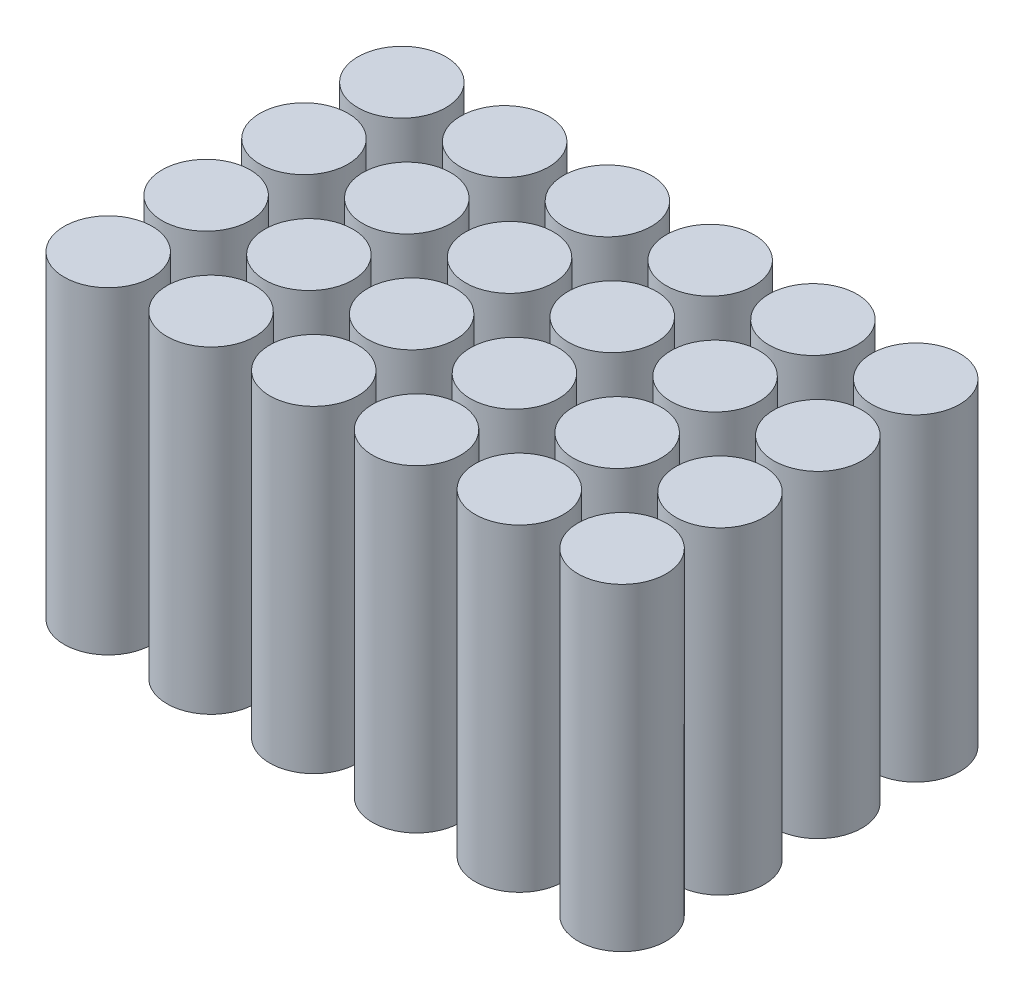
SolidWorks part; units mm, degrees
material "Li-ion 18650 equivalent"
ref_plane "Front Plane" through (0, 0, 0) normal (0, 0, 1) x (1, 0, 0)
ref_plane "Top Plane" through (0, 0, 0) normal (0, 1, 0) x (1, 0, 0)
ref_plane "Right Plane" through (0, 0, 0) normal (1, 0, 0) x (0, 0, -1)
sketch "Sketch2" plane through (0, 0, 0) normal (0, 1, 0) x (1, 0, 0)
  line L0 (0, -38.3676) -> (0, 38.3676) construction
  line L1 (-63.7189, 0) -> (63.7189, 0) construction
  circle A0 centre (-10.5, -10) radius 9
  circle A1 centre (10.5, -10) radius 9
  circle A2 centre (31.5, -10) radius 9
  circle A3 centre (52.5, -10) radius 9
  circle A4 centre (10.5, 10) radius 9
  circle A5 centre (31.5, 10) radius 9
  circle A6 centre (52.5, 10) radius 9
  circle A7 centre (10.5, 30) radius 9
  circle A8 centre (31.5, 30) radius 9
  circle A9 centre (52.5, 30) radius 9
  circle A10 centre (-10.5, 10) radius 9
  circle A11 centre (-10.5, 30) radius 9
  circle A12 centre (-10.5, -30) radius 9
  circle A13 centre (52.5, -30) radius 9
  circle A14 centre (31.5, -30) radius 9
  circle A15 centre (10.5, -30) radius 9
  circle A16 centre (-52.5, -30) radius 9
  circle A17 centre (-52.5, -10) radius 9
  circle A18 centre (-52.5, 10) radius 9
  circle A19 centre (-52.5, 30) radius 9
  circle A20 centre (-31.5, -30) radius 9
  circle A21 centre (-31.5, -10) radius 9
  circle A22 centre (-31.5, 10) radius 9
  circle A23 centre (-31.5, 30) radius 9
  point P4 (0, 0)
  point P8 (0, 0)
  point P9 (-10.5, -1)
  point P10 (-1.5, -10)
  dimension "D1" = 18
  dimension "D2" = 1
  dimension "D3" = 1.5
  dimension "D6" = 60
  dimension "D7" = 21
  dimension "D4" = 4
  dimension "D5" = 3
extrude "Boss-Extrude1" add sketch "Sketch2" along normal blind 65
